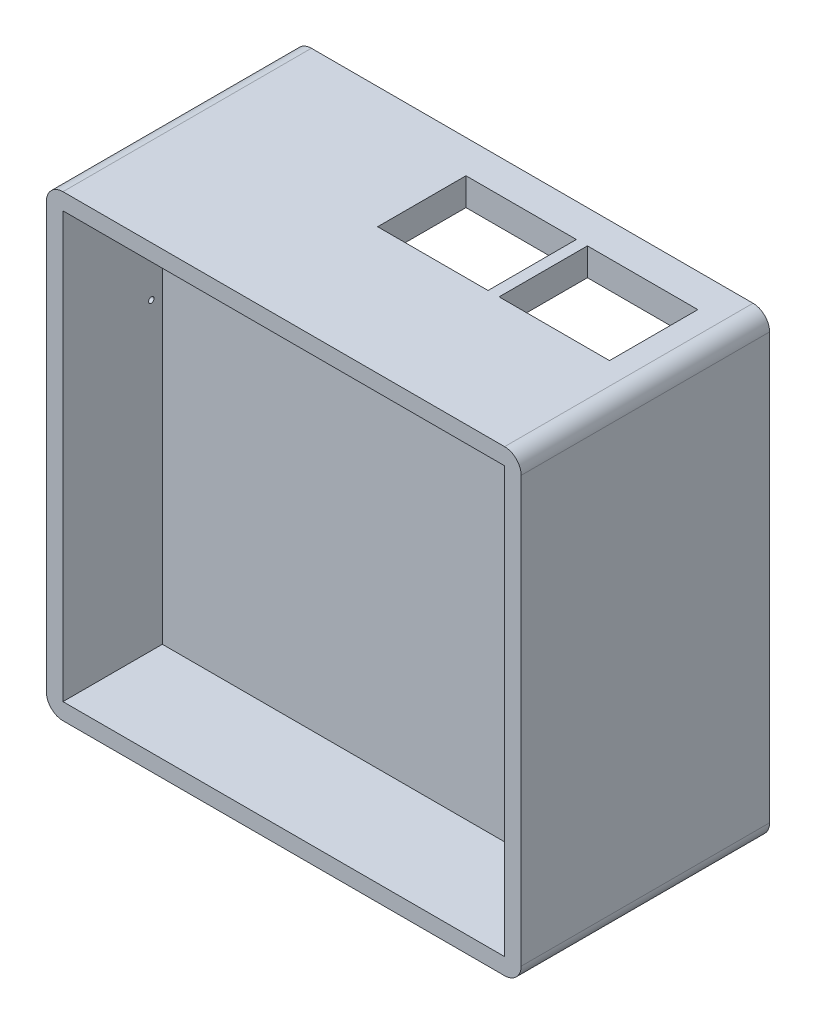
SolidWorks part; units mm, degrees
ref_plane "Plan de face" through (0, 0, 0) normal (0, 0, 1) x (1, 0, 0)
ref_plane "Plan de dessus" through (0, 0, 0) normal (0, 1, 0) x (1, 0, 0)
ref_plane "Plan de droite" through (0, 0, 0) normal (1, 0, 0) x (0, 0, -1)
sketch "Esquisse1" plane through (0, 0, 0) normal (0, 0, 1) x (1, 0, 0)
  line L1 (-40.0742, 28.9918) -> (45.9258, 28.9918)
  line L2 (-40.0742, 28.9918) -> (-40.0742, -54.0082)
  line L3 (-40.0742, -54.0082) -> (45.9258, -54.0082)
  line L4 (45.9258, 28.9918) -> (45.9258, -54.0082)
  dimension "D1" = 86
  dimension "D2" = 83
extrude "Boss.-Extru.1" add sketch "Esquisse1" along normal blind 45
sketch "Esquisse2" plane through (0, 0, 0) normal (0, 0, -1) x (-1, 0, 0)
  line L0 (-45.9258, -54.0082) -> (-45.9258, 28.9918) construction
  line L1 (-43.9258, 26.9918) -> (38.0742, 26.9918)
  line L2 (-43.9258, 26.9918) -> (-43.9258, -52.0082)
  line L3 (-43.9258, -52.0082) -> (38.0742, -52.0082)
  line L4 (38.0742, 26.9918) -> (38.0742, -52.0082)
  line L5 (-45.9258, 28.9918) -> (40.0742, 28.9918) construction
  line L6 (40.0742, 28.9918) -> (40.0742, -54.0082) construction
  line L7 (40.0742, -54.0082) -> (-45.9258, -54.0082) construction
  dimension "D1" = 2
  dimension "D2" = 2
  dimension "D3" = 2
  dimension "D4" = 2
extrude "Enlèv. mat.-Extru.1" cut sketch "Esquisse2" against normal blind 3
sketch "Esquisse3" plane through (0, 0, 3) normal (0, 0, -1) x (-1, 0, 0)
  line L0 (38.0742, -52.0082) -> (38.0742, 26.9918) construction
  line L1 (-40.9258, 23.9918) -> (35.0742, 23.9918)
  line L2 (-40.9258, 23.9918) -> (-40.9258, -49.0082)
  line L3 (-40.9258, -49.0082) -> (35.0742, -49.0082)
  line L4 (35.0742, 23.9918) -> (35.0742, -49.0082)
  line L5 (-43.9258, 26.9918) -> (-43.9258, -52.0082) construction
  line L6 (-43.9258, -52.0082) -> (38.0742, -52.0082) construction
  line L7 (38.0742, 26.9918) -> (-43.9258, 26.9918) construction
  dimension "D1" = 3
  dimension "D2" = 3
  dimension "D3" = 3
  dimension "D4" = 3
extrude "Enlèv. mat.-Extru.2" cut sketch "Esquisse3" against normal blind 20
sketch "Esquisse5" plane through (0, 0, 45) normal (0, 0, 1) x (1, 0, 0)
  line L0 (45.9258, 28.9918) -> (-40.0742, 28.9918) construction
  line L1 (-37.0742, 25.9918) -> (42.9258, 25.9918)
  line L2 (-37.0742, 25.9918) -> (-37.0742, -51.0082)
  line L3 (-37.0742, -51.0082) -> (42.9258, -51.0082)
  line L4 (42.9258, 25.9918) -> (42.9258, -51.0082)
  line L5 (-40.0742, 28.9918) -> (-40.0742, -54.0082) construction
  line L6 (45.9258, -54.0082) -> (45.9258, 28.9918) construction
  line L7 (-40.0742, -54.0082) -> (45.9258, -54.0082) construction
  dimension "D1" = 3
  dimension "D2" = 3
  dimension "D3" = 3
  dimension "D4" = 3
extrude "Enlèv. mat.-Extru.3" cut sketch "Esquisse5" against normal blind 18
sketch3d "Esquisse3D1"
  point P0 (-10.8, -9.7977, 27)
sketch3d "Esquisse3D2"
  point P0 (0.8444, -24.1752, 27)
sketch3d "Esquisse3D3"
  point P0 (-6.8788, -22.9261, 23)
sketch "Esquisse7" plane through (0, 28.9918, 0) normal (0, 1, 0) x (1, 0, 0)
  line L0 (45.9258, -45) -> (45.9258, 0) construction
  line L1 (38.9258, -6) -> (18.9258, -6)
  line L2 (38.9258, -6) -> (38.9258, -22)
  line L3 (38.9258, -22) -> (18.9258, -22)
  line L4 (18.9258, -6) -> (18.9258, -22)
  line L5 (45.9258, 0) -> (-40.0742, 0) construction
  dimension "D1" = 7
  dimension "D2" = 6
  dimension "D3" = 16
  dimension "D4" = 20
extrude "Enlèv. mat.-Extru.4" cut sketch "Esquisse7" against normal blind 18
sketch "Esquisse8" plane through (0, 28.9918, 0) normal (0, 1, 0) x (1, 0, 0)
  line L0 (18.9258, -6) -> (18.9258, -22) construction
  line L1 (16.9258, -6) -> (-3.0742, -6)
  line L2 (16.9258, -6) -> (16.9258, -22)
  line L3 (16.9258, -22) -> (-3.0742, -22)
  line L4 (-3.0742, -6) -> (-3.0742, -22)
  line L5 (45.9258, 0) -> (-40.0742, 0) construction
  dimension "D1" = 2
  dimension "D2" = 6
  dimension "D3" = 20
  dimension "D4" = 16
extrude "Enlèv. mat.-Extru.5" cut sketch "Esquisse8" against normal blind 18
sketch "Esquisse10" plane through (-40.0742, 0, 0) normal (-1, 0, 0) x (0, 0, 1)
  line L0 (45, 28.9918) -> (0, 28.9918) construction
  line L1 (12, -1.0082) -> (22, -1.0082)
  line L2 (12, -1.0082) -> (12, 23.9918)
  line L3 (12, 23.9918) -> (22, 23.9918)
  line L4 (22, -1.0082) -> (22, 23.9918)
  line L5 (0, 28.9918) -> (0, -54.0082) construction
  dimension "D1" = 10
  dimension "D2" = 5
  dimension "D3" = 25
  dimension "D4" = 12
extrude "Enlèv. mat.-Extru.6" cut sketch "Esquisse10" against normal blind 18
sketch "Esquisse12" plane through (-40.0742, 0, 0) normal (-1, 0, 0) x (0, 0, 1)
  line L0 (22, -1.0082) -> (22, 23.9918) construction
  line L1 (12, -1.0082) -> (22, -1.0082) construction
  circle A0 centre (29, 3.9918) radius 0.5
  dimension "D3" = 1
  dimension "D1" = 7
  dimension "D2" = 5
extrude "Enlèv. mat.-Extru.9" cut sketch "Esquisse12" against normal blind 18 contours A0
fillet "Congé2" radius 3 4 edges at (45.9258, -54.0082, 22.5) (-40.0742, -54.0082, 22.5) (-40.0742, 28.9918, 22.5) (45.9258, 28.9918, 22.5)
sketch3d "Esquisse3D4"
  point P0 (-40.0742, -25.4898, 22.8286)
